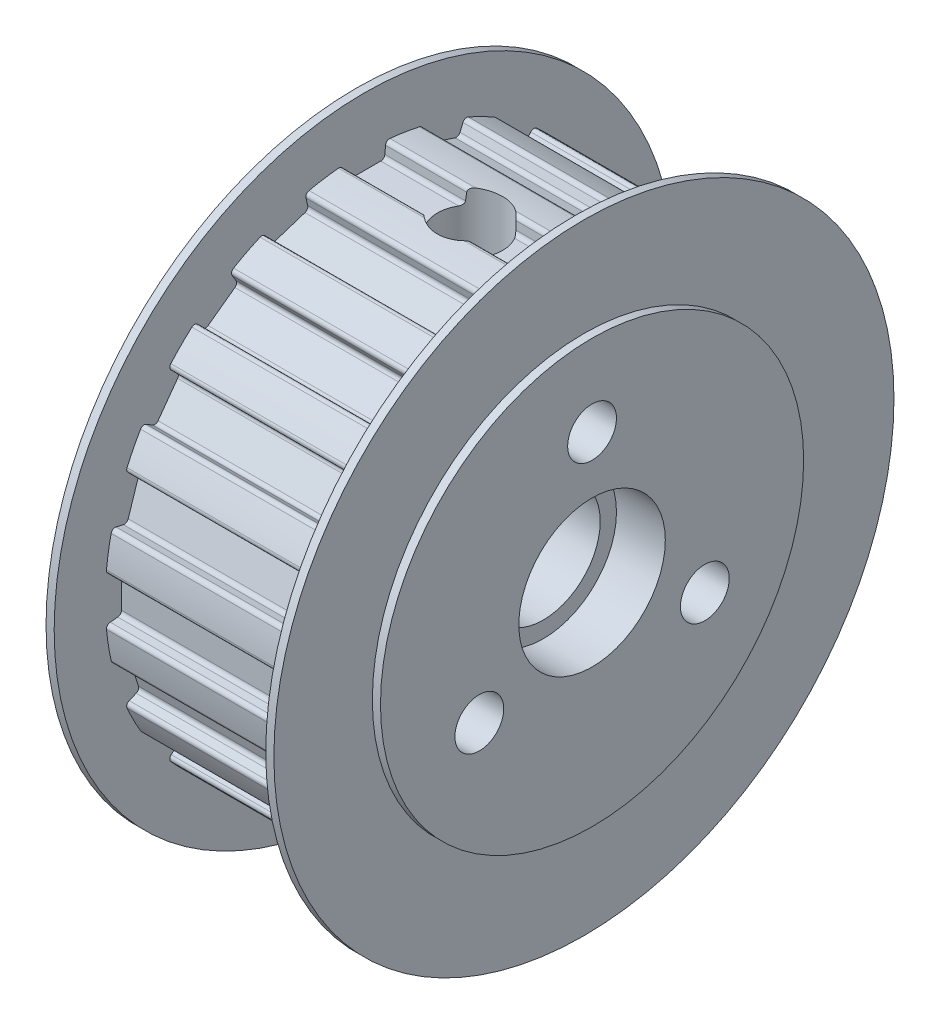
SolidWorks part; units mm, degrees
ref_plane "Plan de face" through (0, 0, 0) normal (0, 0, 1) x (1, 0, 0)
ref_plane "Plan de dessus" through (0, 0, 0) normal (0, 1, 0) x (1, 0, 0)
ref_plane "Plan de droite" through (0, 0, 0) normal (1, 0, 0) x (0, 0, -1)
sketch "Esquisse1" plane through (0, 0, 0) normal (1, 0, 0) x (0, 0, -1)
  circle A0 centre (0, 0) radius 15.915
  dimension "D1" = 31.83
extrude "Extrusion1" add sketch "Esquisse1" along normal blind 13
sketch "Esquisse22" plane through (0, 0, 0) normal (-1, 0, 0) x (0, 0, 1)
  line L0 (0, 0) -> (0, 15.915) construction
  line L1 (-1.25, 14.915) -> (1.25, 14.915)
  line L2 (0, 0) -> (1.25, 14.915) construction
  line L3 (0, 0) -> (-1.25, 14.915) construction
  line L4 (-1.25, 14.915) -> (-2.1271, 25.381)
  line L5 (1.25, 14.915) -> (2.1266, 25.3749)
  line L6 (-2.1271, 25.381) -> (2.1266, 25.3749)
  circle A0 centre (0, 0) radius 15.915 construction
  dimension "D1" = 2.5
  dimension "D2" = 1.25
  dimension "D3" = 1
  dimension "D4" = 180
  dimension "D5" = 180
extrude "Enlèv. mat.-Extru.2" cut sketch "Esquisse22" against normal up to next (13 mm away)
fillet "Congé1" radius 0.25 1 edges at (6.5, 14.915, -1.25)
fillet "Congé2" radius 0.25 1 edges at (6.5, 15.8594, -1.3291)
fillet "Congé3" radius 0.25 1 edges at (6.5, 14.915, 1.25)
fillet "Congé4" radius 0.25 1 edges at (6.5, 15.8594, 1.3291)
pattern_circular "Répétition circulaire1" count 20 over 360 about axis through (0, 0, 0) along (1, 0, 0) of "Enlèv. mat.-Extru.2", "Congé1", "Congé2", "Congé3", "Congé4"
sketch "Esquisse23" plane through (0, 0, 0) normal (-1, 0, 0) x (0, 0, 1)
  circle A0 centre (0, 0) radius 19.05
  dimension "D1" = 38.1
extrude "Extrusion2" add sketch "Esquisse23" along normal blind 1
sketch "Esquisse24" plane through (13, 0, 0) normal (1, 0, 0) x (0, 0, -1)
  circle A0 centre (0, 0) radius 19.05
  dimension "D1" = 38.1
extrude "Extrusion3" add sketch "Esquisse24" along normal blind 1
sketch "Esquisse25" plane through (-1, 0, 0) normal (-1, 0, 0) x (0, 0, 1)
  circle A0 centre (0, 0) radius 3.5
  circle A1 centre (0, 8) radius 1.5
  circle A2 centre (6.9282, -4) radius 1.5
  circle A3 centre (-6.9282, -4) radius 1.5
  dimension "D1" = 7
  dimension "D2" = 8
extrude "Enlèv. mat.-Extru.3" cut sketch "Esquisse25" against normal through all
sketch "Esquisse30" plane through (0, 14.915, 0) normal (0, 1, 0) x (-1, 0, 0)
  line L1 (-13, 0) -> (0, 0) construction
  line L3 (0, -1.0201) -> (0, 1.0201) construction
  circle A0 centre (-6.5, 0) radius 2
  dimension "D2" = 4
  dimension "D1" = 6.5
extrude "Enlèv. mat.-Extru.5" cut sketch "Esquisse30" against normal up to next and the other way through all
sketch "Esquisse31" plane through (-1, 0, 0) normal (-1, 0, 0) x (0, 0, 1)
  circle A0 centre (0, 0) radius 13
  dimension "D1" = 26
extrude "Enlèv. mat.-Extru.6" cut sketch "Esquisse31" against normal blind 0.5 flip side to cut
sketch "Esquisse32" plane through (14, 0, 0) normal (1, 0, 0) x (0, 0, -1)
  circle A0 centre (0, 0) radius 13
  dimension "D1" = 26
extrude "Enlèv. mat.-Extru.7" cut sketch "Esquisse32" against normal blind 0.5 flip side to cut
chamfer "Chanfrein1" distance 0.25 angle 45 1 edges at (14, 0, 3.5)
chamfer "Chanfrein2" distance 0.25 angle 45 1 edges at (-1, 0, 3.5)
sketch "Esquisse33" plane through (14, 0, 0) normal (1, 0, 0) x (0, 0, -1)
  circle A0 centre (0, 0) radius 4.5
extrude "Extrusion4" cut sketch "Esquisse33" against normal blind 3
chamfer "Chanfrein3" distance 1.25 angle 45 3 edges at (-1, -4, -5.4282) (-1, -4, 8.4282) (-1, 8, 1.5)
